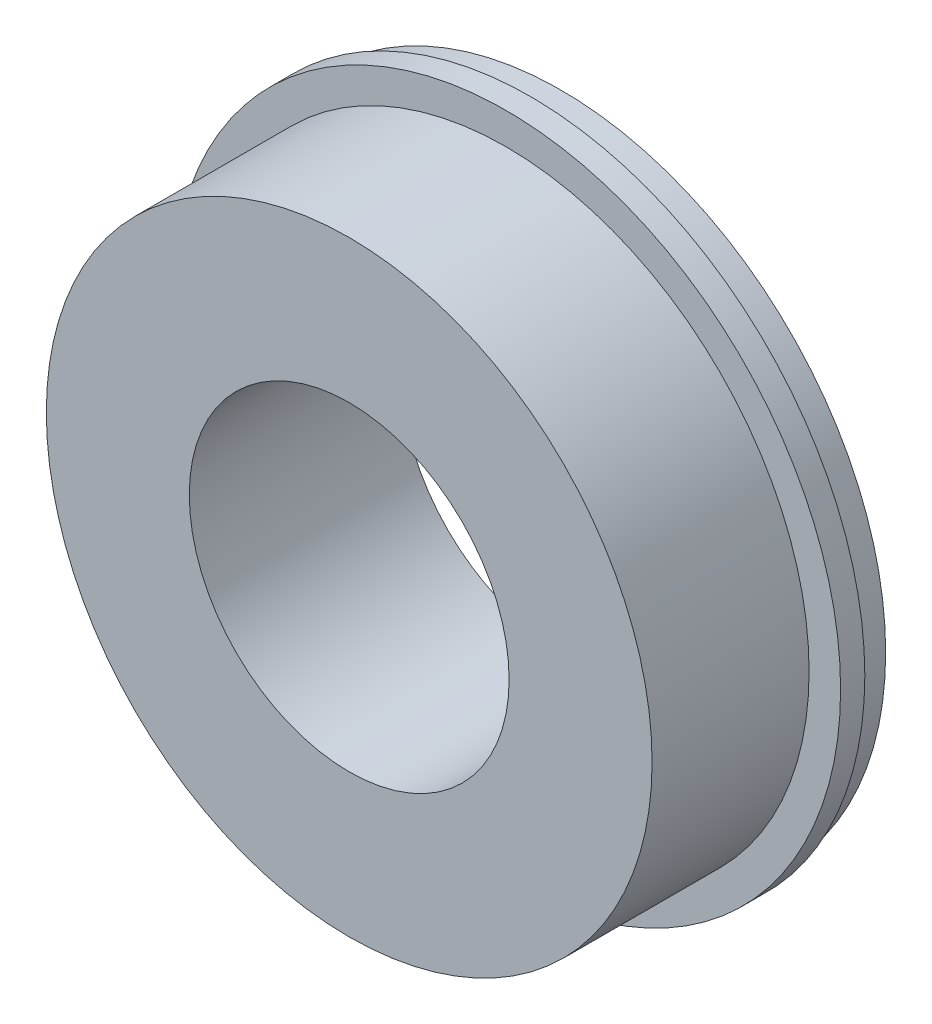
SolidWorks part; units mm, degrees
ref_plane "Front Plane" through (0, 0, 0) normal (0, 0, 1) x (1, 0, 0)
ref_plane "Top Plane" through (0, 0, 0) normal (0, 1, 0) x (1, 0, 0)
ref_plane "Right Plane" through (0, 0, 0) normal (1, 0, 0) x (0, 0, -1)
sketch "Sketch1" plane through (0, 0, 0) normal (0, 0, 1) x (1, 0, 0)
  circle A0 centre (0, 0) radius 70
  dimension "D1" = 140
extrude "Boss-Extrude1" add sketch "Sketch1" along normal mid plane 80
sketch "Sketch2" plane through (0, 0, 0) normal (0, 1, 0) x (1, 0, 0)
  line L0 (0, 0) -> (0, 61.8971) construction
  line L1 (-69, 40) -> (-69, 35)
  line L2 (-69, 35) -> (-67, 35)
  line L3 (-67, 35) -> (-67, 28.7)
  line L4 (-67, 28.7) -> (-60, 28.7)
  line L5 (-60, 28.7) -> (-60, 3.7)
  line L6 (-60, 3.7) -> (-67, 3.7)
  line L7 (-67, 3.7) -> (-67, -2.6)
  line L8 (-67, -2.6) -> (-69, -2.6)
  line L9 (-69, -2.6) -> (-69, -44.7055)
  line L10 (-69, -44.7055) -> (-73.6435, -44.7055)
  line L11 (-73.6435, -44.7055) -> (-73.6435, 40)
  line L12 (-73.6435, 40) -> (-69, 40)
  line L13 (70, 40) -> (-70, 40) construction
  dimension "D1" = 120
  dimension "D2" = 25
  dimension "D3" = 6.3
  dimension "D4" = 6.3
  dimension "D5" = 134
  dimension "D6" = 138
  dimension "D7" = 5
revolve "Cut-Revolve1" cut sketch "Sketch2" angle 360 about L0
sketch "Sketch3" plane through (0, 0, 0) normal (0, 1, 0) x (1, 0, 0)
  line L0 (0, 0) -> (0, -46.5884) construction
  line L2 (-69, -7.6) -> (-62.5, -7.6)
  line L3 (-69, -7.6) -> (-69, -40)
  line L4 (-69, -40) -> (-62.5, -40)
  line L5 (-62.5, -7.6) -> (-62.5, -40)
  line L9 (69, -2.6) -> (-69, -2.6) construction
  line L10 (-69, -40) -> (69, -40) construction
  line L11 (-69, -2.6) -> (-69, -40) construction
  dimension "D1" = 5
  dimension "D2" = 125
revolve "Cut-Revolve2" cut sketch "Sketch3" angle 360 about L0
sketch "Sketch4" plane through (0, 0, 0) normal (0, 1, 0) x (1, 0, 0)
  line L0 (0, 0) -> (0, 53.8059) construction
  line L1 (0, 42.623) -> (-37.5, 42.623)
  line L2 (-37.5, 42.623) -> (-37.5, 20)
  line L3 (-37.5, 20) -> (-33, 20)
  line L4 (-33, 20) -> (-33, -40)
  line L5 (-62.5, -40) -> (62.5, -40) construction
  line L6 (0, 42.623) -> (0, -40)
  line L7 (0, -40) -> (-33, -40)
  dimension "D1" = 60
  dimension "D2" = 66
  dimension "D3" = 75
revolve "Cut-Revolve3" cut sketch "Sketch4" angle 360 about L0
cosmetic thread "Cosmetic Thread1" parameters "D2"=68
sketch "Sketch5" plane through (0, 0, 0) normal (0, 1, 0) x (1, 0, 0)
  line L0 (0, 0) -> (0, 44.7661) construction
  line L1 (-32.9906, 35) -> (-42.25, 35)
  line L2 (-32.9906, 35) -> (-32.9906, 29.5)
  line L3 (-32.9906, 29.5) -> (-42.25, 29.5)
  line L4 (-42.25, 35) -> (-42.25, 29.5)
  line L5 (37.5, 40) -> (-37.5, 40) construction
  dimension "D1" = 5.5
  dimension "D2" = 84.5
  dimension "D3" = 5
revolve "Cut-Revolve4" cut sketch "Sketch5" angle 360 about L0
sketch "Sketch6" plane through (0, 0, 0) normal (0, 1, 0) x (1, 0, 0)
  line L0 (67, 3.7) -> (-67, 3.7) construction
  line L1 (-80.8463, 3.7) -> (75.1718, 3.7)
  line L2 (-80.8463, 3.7) -> (-80.8463, 50.1283)
  line L3 (-80.8463, 50.1283) -> (75.1718, 50.1283)
  line L4 (75.1718, 3.7) -> (75.1718, 50.1283)
extrude "Cut-Extrude1" cut sketch "Sketch6" against normal mid plane 162
